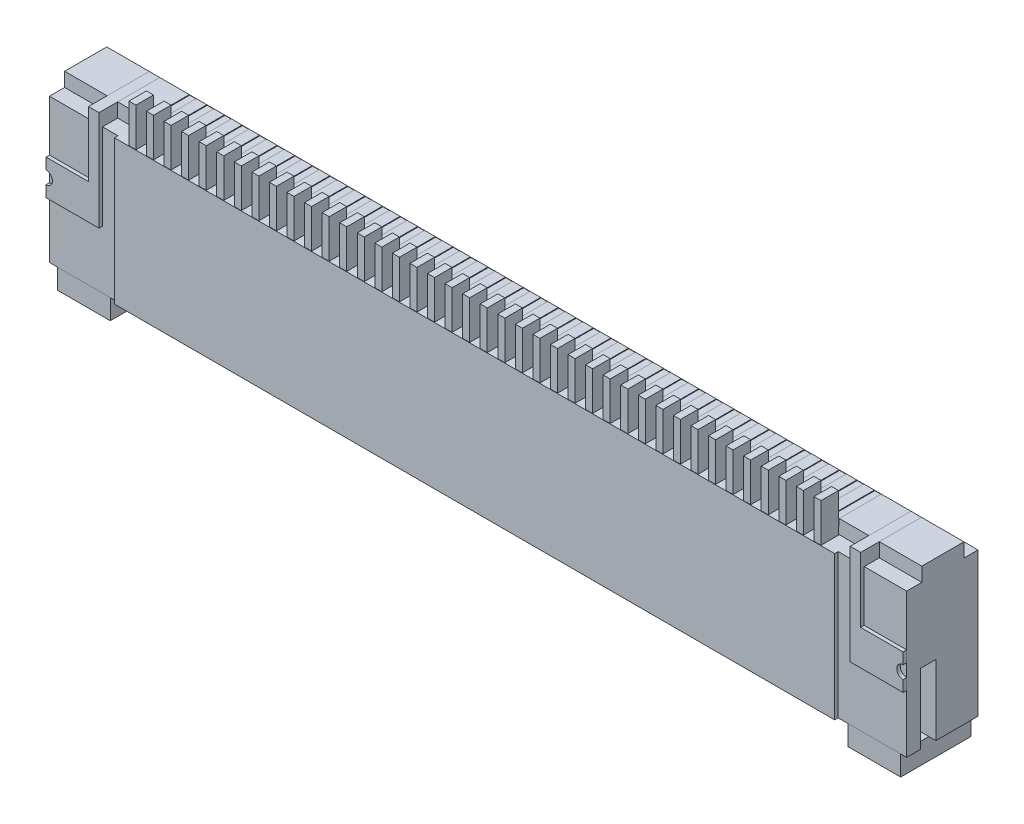
SolidWorks part; units mm, degrees
ref_plane "Plano frontal" through (0, 0, 0) normal (0, 0, 1) x (1, 0, 0)
ref_plane "Plano superior" through (0, 0, 0) normal (0, 1, 0) x (1, 0, 0)
ref_plane "Plano direito" through (0, 0, 0) normal (1, 0, 0) x (0, 0, -1)
sketch "Esboço1" plane through (0, 0, 0) normal (0, 0, 1) x (1, 0, 0)
  line L1 (-12.2, 2.25) -> (12.2, 2.25)
  line L2 (-12.2, 2.25) -> (-12.2, -2.25)
  line L3 (-12.2, -2.25) -> (12.2, -2.25)
  line L4 (12.2, 2.25) -> (12.2, -2.25)
  line L5 (-12.2, 2.25) -> (12.2, -2.25) construction
  line L6 (-12.2, -2.25) -> (12.2, 2.25) construction
  point P0 (0, 0)
  dimension "D1" = 24.4
  dimension "D2" = 4.5
extrude "Ressalto-extrusão1" add sketch "Esboço1" along normal blind 2.13
sketch "Esboço2" plane through (0, 0, 2.13) normal (0, 0, 1) x (1, 0, 0)
  line L1 (12.2, 2.25) -> (-12.2, 2.25) construction
  line L2 (0, -2.875) -> (0, 0) construction
  line L3 (-10.25, 2.25) -> (10.25, 2.25)
  line L4 (-10.25, 2.25) -> (-10.25, -2.25)
  line L5 (-10.25, -2.25) -> (10.25, -2.25)
  line L6 (10.25, 2.25) -> (10.25, -2.25)
  line L7 (-12.2, -2.25) -> (12.2, -2.25) construction
  dimension "D1" = 20.5
extrude "Corte-extrusão1" cut sketch "Esboço2" against normal blind 0.1 flip side to cut
sketch "Esboço3" plane through (0, 0, 0) normal (0, 0, -1) x (-1, 0, 0)
  line L0 (-11.5, -2.25) -> (-11.5, -0.25)
  line L1 (12.2, -2.25) -> (-12.2, -2.25) construction
  line L2 (-11.5, -0.25) -> (-10.3, -0.25)
  line L3 (-10.3, -0.25) -> (-10.3, -0.75)
  line L4 (-10.3, -0.75) -> (10.3, -0.75)
  line L5 (10.3, -0.75) -> (10.3, -0.25)
  line L6 (10.3, -0.25) -> (11.5, -0.25)
  line L7 (11.5, -0.25) -> (11.5, -2.25)
  line L8 (11.5, -2.25) -> (-11.5, -2.25)
  line L9 (-12.2, -2.25) -> (-12.2, 2.25) construction
  line L10 (12.2, 2.25) -> (12.2, -2.25) construction
  line L11 (0, 0) -> (0, -0.75) construction
  dimension "D1" = 0.7
  dimension "D2" = 0.7
  dimension "D3" = 20.6
  dimension "D4" = 2
  dimension "D5" = 1.5
extrude "Corte-extrusão2" cut sketch "Esboço3" against normal offset from surface (1.53 mm away) 0.6 up to face at (0, 0, 2.13)
sketch "Esboço4" plane through (-12.2, 0, 0) normal (-1, 0, 0) x (0, 0, 1)
  line L1 (1.2, -0.25) -> (1.63, -0.25)
  line L2 (1.2, -0.25) -> (1.2, -2.25)
  line L3 (1.2, -2.25) -> (1.63, -2.25)
  line L4 (1.63, -0.25) -> (1.63, -2.25)
  line L5 (2.03, 2.25) -> (2.03, -2.25) construction
  line L6 (0, 2.25) -> (0, -2.25) construction
  line L7 (2.03, -2.25) -> (0, -2.25) construction
  dimension "D1" = 0.4
  dimension "D2" = 1.2
  dimension "D3" = 2
extrude "Corte-extrusão3" cut sketch "Esboço4" against normal through all
sketch "Esboço5" plane through (0, 0, 1.63) normal (0, 0, -1) x (-1, 0, 0)
  line L0 (-12.2, -2.25) -> (12.2, -2.25) construction
  line L1 (11.2, -2.25) -> (10.6, -2.25)
  line L2 (11.2, -2.25) -> (11.2, -0.55)
  line L3 (11.2, -0.55) -> (10.6, -0.55)
  line L4 (10.6, -2.25) -> (10.6, -0.55)
  line L5 (11.5, -2.25) -> (11.5, -0.25) construction
  line L7 (10.3, -0.25) -> (10.3, -0.75) construction
  line L8 (-12.2, -0.25) -> (12.2, -0.25) construction
  line L9 (0, 0) -> (0, 4.9503) construction
  line L10 (-10.6, -2.25) -> (-10.6, -0.55)
  line L11 (-11.2, -0.55) -> (-10.6, -0.55)
  line L12 (-11.2, -2.25) -> (-11.2, -0.55)
  line L13 (-11.2, -2.25) -> (-10.6, -2.25)
  dimension "D1" = 0.3
  dimension "D2" = 0.3
  dimension "D3" = 0.3
extrude "Ressalto-extrusão2" add sketch "Esboço5" along normal blind 0.3
sketch "Esboço6" plane through (0, -2.25, 0) normal (0, -1, 0) x (1, 0, 0)
  line L0 (-11.5, 1.2) -> (-11.5, 0) construction
  line L1 (11.5, 1.2) -> (11.5, 0) construction
  circle A0 centre (-11.5, 0.6) radius 0.2
  circle A1 centre (11.5, 0.6) radius 0.2
  dimension "D1" = 0.4
  dimension "D2" = 0.4
extrude "Corte-extrusão4" cut sketch "Esboço6" against normal up to surface (2 mm away) up to face at (0, -0.25, 0.8717)
sketch "Esboço7" plane through (0, 0, 2.03) normal (0, 0, 1) x (1, 0, 0)
  line L0 (10.25, 2.25) -> (-10.25, 2.25) construction
  line L1 (-12, 2.25) -> (0, 2.25)
  line L2 (-12, 2.25) -> (-12, 2.85)
  line L3 (-10, 3.5) -> (10, 3.5)
  line L4 (-10.25, -2.25) -> (10.25, -2.25) construction
  line L5 (0, 0) -> (0, 3.5) construction
  line L6 (-12, 2.85) -> (-10.5, 2.85)
  line L7 (-10.5, 2.85) -> (-10, 3.5)
  line L8 (-10, 3.5) -> (10, 3.5)
  line L9 (10.5, 2.85) -> (10, 3.5)
  line L10 (12, 2.85) -> (10.5, 2.85)
  line L11 (12, 2.25) -> (12, 2.85)
  line L12 (0, 2.25) -> (12, 2.25)
  line L13 (0, 0) -> (2.2978, 0) construction
  line L14 (-12, -2.25) -> (-12, -2.85)
  line L15 (12, -2.25) -> (12, -2.85)
  line L16 (12, -2.85) -> (10.5, -2.85)
  line L17 (10.5, -2.85) -> (10, -3.5)
  line L18 (-10, -3.5) -> (10, -3.5)
  line L19 (-10.5, -2.85) -> (-10, -3.5)
  line L20 (-12, -2.85) -> (-10.5, -2.85)
  line L21 (-10, -3.5) -> (10, -3.5)
  line L22 (-12, -2.25) -> (-10.25, -2.25)
  line L23 (-10.25, -2.25) -> (-10.25, 2.25)
  line L24 (-10.25, 2.25) -> (-10.25, -2.25) construction
  line L25 (10.25, 2.25) -> (10.25, -2.25)
  line L26 (10.25, -2.25) -> (12, -2.25)
  dimension "D1" = 24
  dimension "D2" = 5.75
  dimension "D3" = 1.5
  dimension "D4" = 0.6
  dimension "D5" = 20
extrude "Ressalto-extrusão3" add sketch "Esboço7" against normal up to surface (2 mm away) from offset 0.03 separate body offset against normal yes
sketch "Esboço8" plane through (0, 0, 0) normal (0, 0, -1) x (-1, 0, 0)
  line L0 (-12.2, 2.25) -> (12.2, 2.25) construction
  line L1 (-10.25, -2.25) -> (10.4244, -2.25)
  line L2 (-10.25, -2.25) -> (-10.25, 2.25)
  line L3 (-10.25, 2.25) -> (10.4244, 2.25)
  line L4 (10.4244, -2.25) -> (10.4244, 2.25)
extrude "Corte-extrusão5" cut sketch "Esboço8" against normal through all
sketch "Esboço10" plane through (0, -3.5, 0) normal (0, -1, 0) x (1, 0, 0)
  line L0 (10.5, 0) -> (10.5, 2) construction
  line L1 (-10.5, 2) -> (10.5, 2)
  line L2 (-10.5, 2) -> (-10.5, 0.6)
  line L3 (-10.5, 0.6) -> (10.5, 0.6)
  line L4 (10.5, 2) -> (10.5, 0.6)
  line L5 (10, 0) -> (-10, 0) construction
  dimension "D1" = 0.6
extrude "Corte-extrusão6" cut sketch "Esboço10" against normal up to surface (0.65 mm away) up to face at (-11.25, -2.85, 1)
sketch "Esboço11" plane through (0, -2.85, 0) normal (0, -1, 0) x (1, 0, 0)
  line L0 (12, 2) -> (-12, 2) construction
  line L1 (-10.5, 0.6) -> (10.5, 0.6)
  line L2 (-10.5, 0.6) -> (-10.5, 2)
  line L3 (-10.5, 2) -> (10.5, 2)
  line L4 (10.5, 0.6) -> (10.5, 2)
  line L5 (10.5, 0) -> (10.5, 0.6) construction
extrude "Corte-extrusão7" cut sketch "Esboço11" against normal through all
sketch "Esboço12" plane through (0, 0, 1.33) normal (0, 0, -1) x (-1, 0, 0)
  line L0 (-12, -2.25) -> (12, -2.25) construction
  line L1 (-11.35, -2.25) -> (-10.45, -2.25)
  line L2 (-11.35, -2.25) -> (-11.35, -0.4)
  line L3 (-11.35, -0.4) -> (-10.45, -0.4)
  line L4 (-10.45, -2.25) -> (-10.45, -0.4)
  line L5 (-11.5, -0.25) -> (-11.5, -2.25) construction
  line L6 (-10.3, -0.25) -> (-11.5, -0.25) construction
  line L7 (-10.3, -0.25) -> (-10.3, -0.75) construction
  line L8 (0, 0) -> (0, -1.3813) construction
  line L9 (10.45, -2.25) -> (10.45, -0.4)
  line L10 (11.35, -0.4) -> (10.45, -0.4)
  line L11 (11.35, -2.25) -> (11.35, -0.4)
  line L12 (11.35, -2.25) -> (10.45, -2.25)
  point P6 (-11.5, -1.25)
  point P11 (-10.3, -0.5)
  dimension "D1" = 0.15
  dimension "D2" = 0.15
  dimension "D3" = 0.15
extrude "Ressalto-extrusão4" add sketch "Esboço12" along normal up to surface (1.3 mm away) from offset 0.03 up to face at (0, -2.8625, 0)
sketch "Esboço13" plane through (0, 0, 0) normal (0, 0, -1) x (-1, 0, 0)
  line L0 (10.45, -2.25) -> (10.45, -0.4) construction
  line L1 (-10.45, -2.25) -> (10.45, -2.25)
  line L2 (-10.45, -2.25) -> (-10.45, -1.95)
  line L3 (-10.45, -1.95) -> (10.45, -1.95)
  line L4 (10.45, -2.25) -> (10.45, -1.95)
  dimension "D1" = 0.3
extrude "Ressalto-extrusão5" add sketch "Esboço13" against normal up to surface (0.6 mm away) up to face at (0, -2.7125, 0.6)
sketch "Esboço14" plane through (0, 0, 1.63) normal (0, 0, -1) x (-1, 0, 0)
  line L0 (0, 0) -> (0, -4.4042) construction
  line L1 (-9.75, -0.75) -> (-9.75, -2.25) construction
  line L2 (10.3, -0.75) -> (-10.3, -0.75) construction
  line L3 (9.75, -0.75) -> (9.75, -3.7346) construction
  line L4 (-9.85, -0.75) -> (-9.85, -2.25)
  line L5 (-9.65, -0.75) -> (-9.65, -2.25)
  line L6 (-9.65, -0.75) -> (-9.85, -0.75)
  line L7 (-9.85, -2.25) -> (-9.65, -2.25)
  line L9 (-9.65, -0.75) -> (-9.65, -3.7346) construction
  line L10 (-9.75, -0.75) -> (-9.75, -3.7346) construction
  line L11 (-9.85, -0.75) -> (-9.85, -3.7346) construction
  line L12 (-10.6, -2.25) -> (10.6, -2.25) construction
  dimension "D1" = 19.5
  dimension "D2" = 0.1
  dimension "D3" = 0.1
extrude "Ressalto-extrusão6" add sketch "Esboço14" along normal blind 0.5 separate body
pattern_linear "Padrão linear1" count 40 spacing 0.5 along (-1, 0, 0) of bodies 113
sketch "Esboço16" plane through (0, 0, 0) normal (0, 0, -1) x (-1, 0, 0)
  line L0 (-9.65, -2.25) -> (-9.65, -0.75) construction
  line L1 (-9.85, -0.75) -> (-9.85, -2.25) construction
  line L2 (-9.65, -2.25) -> (-9.65, -0.75)
  line L3 (-9.85, -0.75) -> (-9.85, -2.25)
  line L4 (-9.85, -2.25) -> (-9.65, -2.25)
  line L5 (-9.35, -2.25) -> (-9.15, -2.25)
  line L6 (-9.35, -0.75) -> (-9.35, -2.25)
  line L7 (-9.15, -2.25) -> (-9.15, -0.75)
  line L8 (-8.85, -2.25) -> (-8.65, -2.25)
  line L9 (-8.85, -0.75) -> (-8.85, -2.25)
  line L10 (-8.65, -2.25) -> (-8.65, -0.75)
  line L11 (-8.35, -2.25) -> (-8.15, -2.25)
  line L12 (-8.35, -0.75) -> (-8.35, -2.25)
  line L13 (-8.15, -2.25) -> (-8.15, -0.75)
  line L14 (-7.85, -2.25) -> (-7.65, -2.25)
  line L15 (-7.85, -0.75) -> (-7.85, -2.25)
  line L16 (-7.65, -2.25) -> (-7.65, -0.75)
  line L17 (-7.35, -2.25) -> (-7.15, -2.25)
  line L18 (-7.35, -0.75) -> (-7.35, -2.25)
  line L19 (-7.15, -2.25) -> (-7.15, -0.75)
  line L20 (-6.85, -2.25) -> (-6.65, -2.25)
  line L21 (-6.85, -0.75) -> (-6.85, -2.25)
  line L22 (-6.65, -2.25) -> (-6.65, -0.75)
  line L23 (-6.35, -2.25) -> (-6.15, -2.25)
  line L24 (-6.35, -0.75) -> (-6.35, -2.25)
  line L25 (-6.15, -2.25) -> (-6.15, -0.75)
  line L26 (-5.85, -2.25) -> (-5.65, -2.25)
  line L27 (-5.85, -0.75) -> (-5.85, -2.25)
  line L28 (-5.65, -2.25) -> (-5.65, -0.75)
  line L29 (-5.35, -2.25) -> (-5.15, -2.25)
  line L30 (-5.35, -0.75) -> (-5.35, -2.25)
  line L31 (-5.15, -2.25) -> (-5.15, -0.75)
  line L32 (-4.85, -2.25) -> (-4.65, -2.25)
  line L33 (-4.85, -0.75) -> (-4.85, -2.25)
  line L34 (-4.65, -2.25) -> (-4.65, -0.75)
  line L35 (-4.35, -2.25) -> (-4.15, -2.25)
  line L36 (-4.35, -0.75) -> (-4.35, -2.25)
  line L37 (-4.15, -2.25) -> (-4.15, -0.75)
  line L38 (-3.85, -2.25) -> (-3.65, -2.25)
  line L39 (-3.85, -0.75) -> (-3.85, -2.25)
  line L40 (-3.65, -2.25) -> (-3.65, -0.75)
  line L41 (-3.35, -2.25) -> (-3.15, -2.25)
  line L42 (-3.35, -0.75) -> (-3.35, -2.25)
  line L43 (-3.15, -2.25) -> (-3.15, -0.75)
  line L44 (-2.85, -2.25) -> (-2.65, -2.25)
  line L45 (-2.85, -0.75) -> (-2.85, -2.25)
  line L46 (-2.65, -2.25) -> (-2.65, -0.75)
  line L47 (-2.35, -2.25) -> (-2.15, -2.25)
  line L48 (-2.35, -0.75) -> (-2.35, -2.25)
  line L49 (-2.15, -2.25) -> (-2.15, -0.75)
  line L50 (-1.85, -2.25) -> (-1.65, -2.25)
  line L51 (-1.85, -0.75) -> (-1.85, -2.25)
  line L52 (-1.65, -2.25) -> (-1.65, -0.75)
  line L53 (-1.35, -2.25) -> (-1.15, -2.25)
  line L54 (-1.35, -0.75) -> (-1.35, -2.25)
  line L55 (-1.15, -2.25) -> (-1.15, -0.75)
  line L56 (-0.85, -2.25) -> (-0.65, -2.25)
  line L57 (-0.85, -0.75) -> (-0.85, -2.25)
  line L58 (-0.65, -2.25) -> (-0.65, -0.75)
  line L59 (-0.35, -2.25) -> (-0.15, -2.25)
  line L60 (-0.35, -0.75) -> (-0.35, -2.25)
  line L61 (-0.15, -2.25) -> (-0.15, -0.75)
  line L62 (0.15, -2.25) -> (0.35, -2.25)
  line L63 (0.15, -0.75) -> (0.15, -2.25)
  line L64 (0.35, -2.25) -> (0.35, -0.75)
  line L65 (0.65, -2.25) -> (0.85, -2.25)
  line L66 (0.65, -0.75) -> (0.65, -2.25)
  line L67 (0.85, -2.25) -> (0.85, -0.75)
  line L68 (1.15, -2.25) -> (1.35, -2.25)
  line L69 (1.15, -0.75) -> (1.15, -2.25)
  line L70 (1.35, -2.25) -> (1.35, -0.75)
  line L71 (1.65, -2.25) -> (1.85, -2.25)
  line L72 (1.65, -0.75) -> (1.65, -2.25)
  line L73 (1.85, -2.25) -> (1.85, -0.75)
  line L74 (2.15, -2.25) -> (2.35, -2.25)
  line L75 (2.15, -0.75) -> (2.15, -2.25)
  line L76 (2.35, -2.25) -> (2.35, -0.75)
  line L77 (2.65, -2.25) -> (2.85, -2.25)
  line L78 (2.65, -0.75) -> (2.65, -2.25)
  line L79 (2.85, -2.25) -> (2.85, -0.75)
  line L80 (3.15, -2.25) -> (3.35, -2.25)
  line L81 (3.15, -0.75) -> (3.15, -2.25)
  line L82 (3.35, -2.25) -> (3.35, -0.75)
  line L83 (3.65, -2.25) -> (3.85, -2.25)
  line L84 (3.65, -0.75) -> (3.65, -2.25)
  line L85 (3.85, -2.25) -> (3.85, -0.75)
  line L86 (4.15, -2.25) -> (4.35, -2.25)
  line L87 (4.15, -0.75) -> (4.15, -2.25)
  line L88 (4.35, -2.25) -> (4.35, -0.75)
  line L89 (4.65, -2.25) -> (4.85, -2.25)
  line L90 (4.65, -0.75) -> (4.65, -2.25)
  line L91 (4.85, -2.25) -> (4.85, -0.75)
  line L92 (5.15, -2.25) -> (5.35, -2.25)
  line L93 (5.15, -0.75) -> (5.15, -2.25)
  line L94 (5.35, -2.25) -> (5.35, -0.75)
  line L95 (5.65, -2.25) -> (5.85, -2.25)
  line L96 (5.65, -0.75) -> (5.65, -2.25)
  line L97 (5.85, -2.25) -> (5.85, -0.75)
  line L98 (6.15, -2.25) -> (6.35, -2.25)
  line L99 (6.15, -0.75) -> (6.15, -2.25)
  line L100 (6.35, -2.25) -> (6.35, -0.75)
  line L101 (6.65, -2.25) -> (6.85, -2.25)
  line L102 (6.65, -0.75) -> (6.65, -2.25)
  line L103 (6.85, -2.25) -> (6.85, -0.75)
  line L104 (7.15, -2.25) -> (7.35, -2.25)
  line L105 (7.15, -0.75) -> (7.15, -2.25)
  line L106 (7.35, -2.25) -> (7.35, -0.75)
  line L107 (7.65, -2.25) -> (7.85, -2.25)
  line L108 (7.65, -0.75) -> (7.65, -2.25)
  line L109 (7.85, -2.25) -> (7.85, -0.75)
  line L110 (8.15, -2.25) -> (8.35, -2.25)
  line L111 (8.15, -0.75) -> (8.15, -2.25)
  line L112 (8.35, -2.25) -> (8.35, -0.75)
  line L113 (8.65, -2.25) -> (8.85, -2.25)
  line L114 (8.65, -0.75) -> (8.65, -2.25)
  line L115 (8.85, -2.25) -> (8.85, -0.75)
  line L116 (9.15, -2.25) -> (9.35, -2.25)
  line L117 (9.15, -0.75) -> (9.15, -2.25)
  line L118 (9.35, -2.25) -> (9.35, -0.75)
  line L119 (9.65, -2.25) -> (9.85, -2.25)
  line L120 (9.65, -0.75) -> (9.65, -2.25)
  line L121 (9.85, -2.25) -> (9.85, -0.75)
  line L122 (-9.85, -0.75) -> (-9.65, -0.75)
  line L123 (9.65, -0.75) -> (9.85, -0.75)
  line L124 (9.15, -0.75) -> (9.35, -0.75)
  line L125 (8.65, -0.75) -> (8.85, -0.75)
  line L126 (8.15, -0.75) -> (8.35, -0.75)
  line L127 (7.65, -0.75) -> (7.85, -0.75)
  line L128 (6.65, -0.75) -> (6.85, -0.75)
  line L129 (7.15, -0.75) -> (7.35, -0.75)
  line L130 (6.15, -0.75) -> (6.35, -0.75)
  line L131 (5.65, -0.75) -> (5.85, -0.75)
  line L132 (5.15, -0.75) -> (5.35, -0.75)
  line L133 (4.65, -0.75) -> (4.85, -0.75)
  line L134 (4.15, -0.75) -> (4.35, -0.75)
  line L135 (3.65, -0.75) -> (3.85, -0.75)
  line L136 (3.15, -0.75) -> (3.35, -0.75)
  line L137 (2.65, -0.75) -> (2.85, -0.75)
  line L138 (2.15, -0.75) -> (2.35, -0.75)
  line L139 (1.65, -0.75) -> (1.85, -0.75)
  line L140 (1.15, -0.75) -> (1.35, -0.75)
  line L141 (0.65, -0.75) -> (0.85, -0.75)
  line L142 (0.15, -0.75) -> (0.35, -0.75)
  line L143 (-0.35, -0.75) -> (-0.15, -0.75)
  line L144 (-0.85, -0.75) -> (-0.65, -0.75)
  line L145 (-1.35, -0.75) -> (-1.15, -0.75)
  line L146 (-1.85, -0.75) -> (-1.65, -0.75)
  line L147 (-2.35, -0.75) -> (-2.15, -0.75)
  line L148 (-2.85, -0.75) -> (-2.65, -0.75)
  line L149 (-3.35, -0.75) -> (-3.15, -0.75)
  line L150 (-3.85, -0.75) -> (-3.65, -0.75)
  line L151 (-4.35, -0.75) -> (-4.15, -0.75)
  line L152 (-4.85, -0.75) -> (-4.65, -0.75)
  line L153 (-5.35, -0.75) -> (-5.15, -0.75)
  line L154 (-5.85, -0.75) -> (-5.65, -0.75)
  line L155 (-6.35, -0.75) -> (-6.15, -0.75)
  line L156 (-6.85, -0.75) -> (-6.65, -0.75)
  line L157 (-7.35, -0.75) -> (-7.15, -0.75)
  line L158 (-7.85, -0.75) -> (-7.65, -0.75)
  line L159 (-8.35, -0.75) -> (-8.15, -0.75)
  line L160 (-8.85, -0.75) -> (-8.65, -0.75)
  line L161 (-9.35, -0.75) -> (-9.15, -0.75)
  dimension "D1" = 40
extrude "Ressalto-extrusão8" add sketch "Esboço16" against normal blind 0.5 from offset 0.03 offset against normal yes
sketch "Esboço17" plane through (12.2, 0, 0) normal (1, 0, 0) x (0, 0, -1)
  line L0 (0, -2.25) -> (0, 2.25) construction
  line L1 (-0.4, 2.65) -> (0.4, 2.65)
  line L2 (-0.4, 2.65) -> (-0.4, 1.85)
  line L3 (-0.4, 1.85) -> (0.4, 1.85)
  line L4 (0.4, 2.65) -> (0.4, 1.85)
  line L5 (-0.4, 2.65) -> (0.4, 1.85) construction
  line L6 (-0.4, 1.85) -> (0.4, 2.65) construction
  line L7 (-2.46, 2.65) -> (-1.6, 2.65)
  line L8 (-2.46, 2.65) -> (-2.46, 1.85)
  line L9 (-2.46, 1.85) -> (-1.6, 1.85)
  line L10 (-1.6, 2.65) -> (-1.6, 1.85)
  line L11 (-2.46, 2.65) -> (-1.6, 1.85) construction
  line L12 (-2.46, 1.85) -> (-1.6, 2.65) construction
  line L13 (-2.03, 2.25) -> (0, 2.25) construction
  point P0 (0, 2.25)
  point P6 (-2.03, 2.25)
  dimension "D1" = 1.2
  dimension "D2" = 0.4
  dimension "D3" = 0.4
  dimension "D4" = 0.4
extrude "Corte-extrusão8" cut sketch "Esboço17" against normal through all
sketch "Esboço19" plane through (0, 0, 2.13) normal (0, 0, 1) x (1, 0, 0)
  line L0 (-12.2, 1.85) -> (-12.2, -2.25) construction
  line L1 (-12.2, 0.4) -> (-10.9908, 0.4)
  line L2 (-12.2, 0.4) -> (-12.2, -0.6)
  line L3 (-12.2, -0.6) -> (-10.9908, -0.6)
  line L4 (-10.9908, 0.4) -> (-10.9908, -0.6)
  line L5 (-12.2, 2.25) -> (12.2, 2.25) construction
  line L6 (-10.9908, -0.6) -> (-10.6908, -0.6)
  line L7 (-10.9908, -0.6) -> (-10.9908, 2.25)
  line L8 (-10.9908, 2.25) -> (-10.6908, 2.25)
  line L9 (-10.6908, -0.6) -> (-10.6908, 2.25)
  dimension "D1" = 1
  dimension "D2" = 2.85
  dimension "D3" = 0.3
sketch "Esboço20" plane through (0, 0, 1.6) normal (0, 0, 1) x (1, 0, 0)
  line L0 (-10.6908, -0.6) -> (-10.6908, 2.25) construction
  line L1 (-10.9908, 2.25) -> (-10.6908, 2.25)
  line L2 (-10.9908, 2.25) -> (-10.9908, 1.95)
  line L3 (-10.9908, 1.95) -> (-10.6908, 1.95)
  line L4 (-10.6908, 2.25) -> (-10.6908, 1.95)
  dimension "D1" = 0.3
extrude "Corte-extrusão9" cut sketch "Esboço20" against normal blind 10
mirror "Espelhar1" about plane through (0, 0, 0) normal (1, 0, 0) of "Corte-extrusão9"
extrude "Ressalto-extrusão9" add sketch "Esboço19" against normal up to surface (0.1 mm away) separate body contours L4 L1 L2 L3 | L6 L9 L8 L7 L4 up to face at (-11.225, -0.2, 2.03)
sketch "Esboço21" plane through (0, 0, 2.03) normal (0, 0, -1) x (-1, 0, 0)
  line L0 (10.9908, 2.25) -> (10.9908, 0.4) construction
  line L1 (10.6908, 2.25) -> (10.9908, 2.25)
  line L2 (10.6908, 2.25) -> (10.6908, 1.85)
  line L3 (10.6908, 1.85) -> (10.9908, 1.85)
  line L4 (10.9908, 2.25) -> (10.9908, 1.85)
  line L5 (12.2, 1.85) -> (10.25, 1.85) construction
extrude "Ressalto-extrusão10" add sketch "Esboço21" along normal up to surface (0.43 mm away) up to face at (0, 2.0833, 1.6)
sketch "Esboço22" plane through (0, 0, 1.6) normal (0, 0, -1) x (-1, 0, 0)
  line L0 (10.6908, 1.95) -> (10.6908, 2.25) construction
  line L1 (10.9908, 1.95) -> (10.6908, 1.95) construction
  line L2 (10.9908, 2.25) -> (10.9908, 1.95) construction
  line L3 (10.6908, 1.95) -> (10.6908, 2.25)
  line L4 (10.9908, 1.95) -> (10.6908, 1.95)
  line L5 (10.9908, 2.25) -> (10.9908, 1.95)
  line L6 (10.9908, 2.25) -> (10.6908, 2.25) construction
  line L7 (10.9908, 2.25) -> (10.6908, 2.25)
extrude "Ressalto-extrusão11" add sketch "Esboço22" along normal up to surface (1.2 mm away) up to face at (0, 2.0833, 0.4)
sketch "Esboço23" plane through (0, 0, 2.13) normal (0, 0, 1) x (1, 0, 0)
  line L0 (-12.2, 0.4) -> (-12.2, -0.6) construction
  circle A0 centre (-12.2, -0.1) radius 0.1829
extrude "Corte-extrusão10" cut sketch "Esboço23" against normal blind 10
mirror "Espelhar2" about plane through (0, 0, 0) normal (1, 0, 0) of bodies 161
sketch "Esboço24" plane through (0, 0, 2.13) normal (0, 0, 1) x (1, 0, 0)
  line L0 (-10.25, 1.85) -> (10.25, 1.85) construction
  line L1 (-9.85, 1.85) -> (-9.65, 1.85)
  line L2 (-9.85, 1.85) -> (-9.85, 2.95)
  line L3 (-9.85, 2.95) -> (-9.65, 2.95)
  line L4 (-9.65, 1.85) -> (-9.65, 2.95)
  line L5 (0, 0) -> (0, 4.6196) construction
  line L6 (-9.75, 2.95) -> (-9.75, 1.85) construction
  line L7 (-10.6908, 2.25) -> (10.6908, 2.25) construction
  dimension "D1" = 0.2
  dimension "D2" = 19.5
  dimension "D3" = 0.7
extrude "Ressalto-extrusão12" add sketch "Esboço24" against normal blind 0.5 from offset 0.01 offset against normal yes
pattern_linear "Padrão linear2" count 40 spacing 0.5 along (1, 0, 0) of "Ressalto-extrusão12"
sketch "Esboço25" plane through (0, 2.25, 0) normal (0, 1, 0) x (1, 0, 0)
  line L0 (-12.2, -0.4) -> (12.2, -0.4) construction
  line L1 (-9.85, -1.62) -> (-9.65, -1.62)
  line L2 (-9.85, -1.62) -> (-9.85, -0.4)
  line L3 (-9.85, -0.4) -> (-9.65, -0.4)
  line L4 (-9.65, -1.62) -> (-9.65, -0.4)
  line L5 (-9.65, -1.62) -> (-9.65, -2.12) construction
extrude "Corte-extrusão11" cut sketch "Esboço25" against normal blind 0.2
pattern_linear "Padrão linear3" count 40 spacing 0.5 along (1, 0, 0) of "Corte-extrusão11"
sketch "Esboço27" plane through (0, 0, 1.62) normal (0, 0, -1) x (-1, 0, 0)
  line L0 (9.66, 2.24) -> (9.84, 2.24)
  line L1 (9.65, 2.05) -> (9.85, 2.05)
  line L2 (9.65, 2.05) -> (9.65, 2.25)
  line L3 (9.65, 2.25) -> (9.85, 2.25)
  line L4 (9.85, 2.05) -> (9.85, 2.25)
  line L5 (9.84, 2.06) -> (9.84, 2.24)
  line L6 (9.66, 2.06) -> (9.84, 2.06)
  line L7 (9.66, 2.06) -> (9.66, 2.24)
  dimension "D1" = 0.01
extrude "Ressalto-extrusão14" add sketch "Esboço27" along normal up to surface (1.22 mm away) contours L7 L6 L5 L0 up to face at (0, 2.1453, 0.4)
pattern_linear "Padrão linear4" count 40 spacing 0.5 along (1, 0, 0) of "Ressalto-extrusão14"
